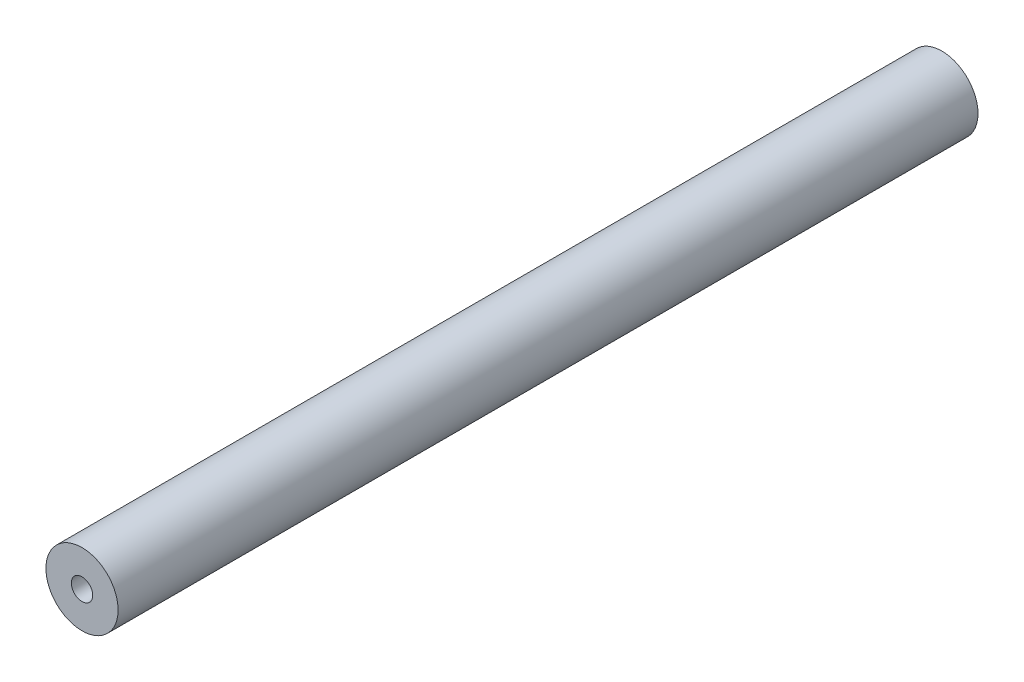
SolidWorks part; units mm, degrees
material "6061-T6 (SS)"
ref_plane "Front Plane" through (0, 0, 0) normal (0, 0, 1) x (1, 0, 0)
ref_plane "Top Plane" through (0, 0, 0) normal (0, 1, 0) x (1, 0, 0)
ref_plane "Right Plane" through (0, 0, 0) normal (1, 0, 0) x (0, 0, -1)
sketch "Sketch1" plane through (0, 0, 0) normal (0, 0, 1) x (1, 0, 0)
  circle A0 centre (0, 0) radius 6.4
  dimension "D1" = 12.8
extrude "Boss-Extrude1" add sketch "Sketch1" along normal blind 152.53
hole_wizard "#10-24 Tapped Hole1" positions "Sketch2" profile "Sketch3" tap size "#10-24" standard "ANSI Inch"
sketch "Sketch2" plane through (0, 0, 0) normal (0, 0, -1) x (-1, 0, 0)
  point P0 (0, 0)
sketch "Sketch3" plane through (0, 0, 0) normal (1, 0, 0) x (0, 1, 0)
  line L0 (0, 0) -> (0, 13.9708)
  line L1 (0, 13.9708) -> (1.8986, 12.83)
  line L2 (1.8986, 12.83) -> (1.8986, 0)
  line L5 (1.8986, 0) -> (0, 0)
  line L10 (0, 13.9708) -> (-1.8987, 12.83) construction
  line L11 (0, -6.35) -> (0, 107.95) construction
  dimension "Tap Drill Dia." = 3.7973
  dimension "Tap Drill Depth" = 12.83
  dimension "Drill Angle" = 118
hole_wizard "#10-24 Tapped Hole2" positions "Sketch4" profile "Sketch5" tap size "#10-24" standard "ANSI Inch"
sketch "Sketch4" plane through (0, 0, 152.53) normal (0, 0, 1) x (1, 0, 0)
  point P0 (0, 0)
sketch "Sketch5" plane through (0, 0, 152.53) normal (1, 0, 0) x (0, -1, 0)
  line L0 (0, 0) -> (0, 13.9708)
  line L1 (0, 13.9708) -> (1.8986, 12.83)
  line L2 (1.8986, 12.83) -> (1.8986, 0)
  line L5 (1.8986, 0) -> (0, 0)
  line L10 (0, 13.9708) -> (-1.8987, 12.83) construction
  line L11 (0, -6.35) -> (0, 107.95) construction
  dimension "Tap Drill Dia." = 3.7973
  dimension "Tap Drill Depth" = 12.83
  dimension "Drill Angle" = 118
